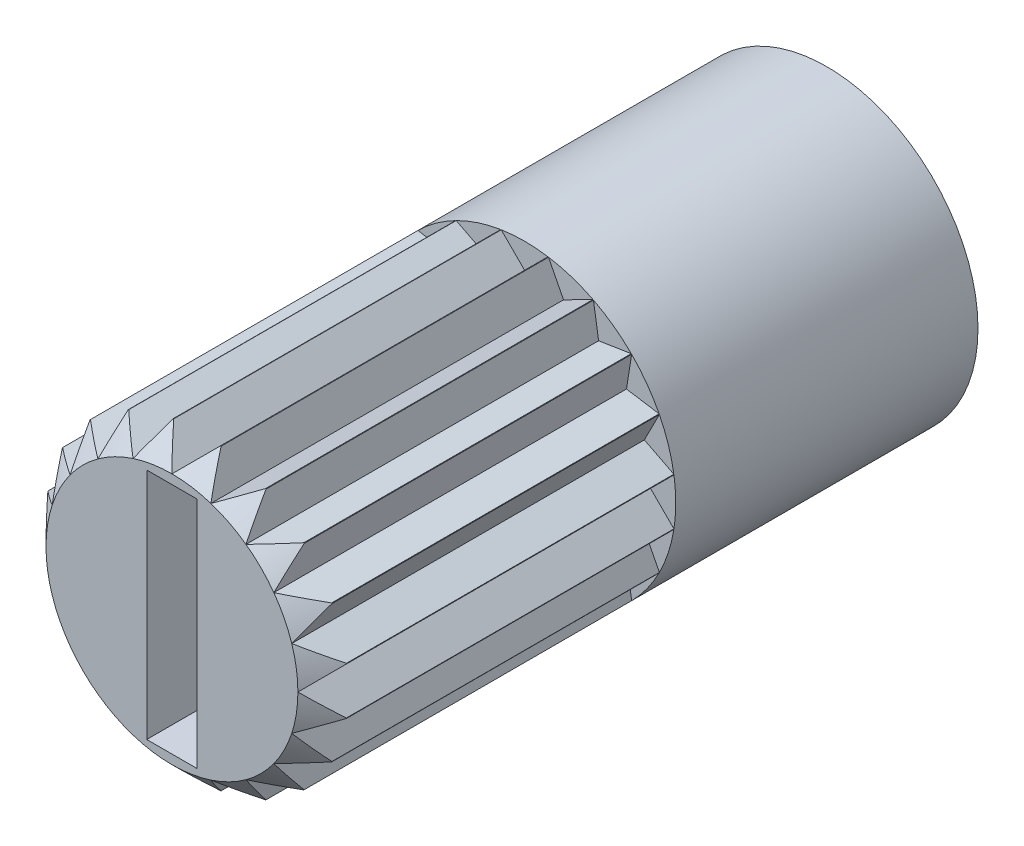
SolidWorks part; units mm, degrees
ref_plane "Plan de face" through (0, 0, 0) normal (0, 0, 1) x (1, 0, 0)
ref_plane "Plan de dessus" through (0, 0, 0) normal (0, 1, 0) x (1, 0, 0)
ref_plane "Plan de droite" through (0, 0, 0) normal (1, 0, 0) x (0, 0, -1)
sketch "Esquisse1" plane through (0, 0, 0) normal (0, 0, 1) x (1, 0, 0)
  circle A0 centre (0, 0) radius 3
  dimension "D1" = 6
extrude "Boss.-Extru.1" add sketch "Esquisse1" along normal blind 3 and the other way blind 10
sketch "Esquisse3" plane through (0, 0, 3) normal (0, 0, 1) x (1, 0, 0)
  line L0 (0, -3.4377) -> (0, 2.4248) construction
  line L1 (-3.9874, 0) -> (3.549, 0) construction
  line L2 (-0.5, 2.3162) -> (0.5, 2.3162)
  line L3 (-0.5, 2.3162) -> (-0.5, -2.3162)
  line L4 (-0.5, -2.3162) -> (0.5, -2.3162)
  line L5 (0.5, 2.3162) -> (0.5, -2.3162)
  dimension "D1" = 1
  dimension "D2" = 0.1086
extrude "Enlèv. mat.-Extru.2" cut sketch "Esquisse3" against normal blind 1.5
chamfer "Chanfrein1" distance 0.5 1 edges at (3, 0, 3)
sketch "Esquisse4" plane through (0, 0, 3) normal (0, 0, 1) x (1, 0, 0)
  line L0 (-3.6113, 0) -> (3.6829, 0) construction
  line L1 (-2.9705, -0.4705) -> (-2.5, 0)
  line L2 (-2.5, 0) -> (-2.9705, 0.4705)
  line L3 (-2.3776, 0.7725) -> (-2.6797, 1.3654)
  line L4 (-2.9705, 0.4705) -> (-2.3776, 0.7725)
  line L5 (-2.0225, 1.4695) -> (-2.1266, 2.1266)
  line L6 (-2.6797, 1.3654) -> (-2.0225, 1.4695)
  line L7 (-1.4695, 2.0225) -> (-1.3654, 2.6797)
  line L8 (-2.1266, 2.1266) -> (-1.4695, 2.0225)
  line L10 (-1.3654, 2.6797) -> (-0.7725, 2.3776)
  line L11 (0, 2.5) -> (0.4705, 2.9705)
  line L12 (-0.4705, 2.9705) -> (0, 2.5)
  line L13 (0.7725, 2.3776) -> (1.3654, 2.6797)
  line L14 (0.4705, 2.9705) -> (0.7725, 2.3776)
  line L15 (1.4695, 2.0225) -> (2.1266, 2.1266)
  line L16 (1.3654, 2.6797) -> (1.4695, 2.0225)
  line L17 (2.0225, 1.4695) -> (2.6797, 1.3654)
  line L18 (2.1266, 2.1266) -> (2.0225, 1.4695)
  line L19 (2.3776, 0.7725) -> (2.9705, 0.4705)
  line L20 (2.6797, 1.3654) -> (2.3776, 0.7725)
  line L21 (2.5, 0) -> (2.9705, -0.4705)
  line L22 (2.9705, 0.4705) -> (2.5, 0)
  line L23 (2.3776, -0.7725) -> (2.6797, -1.3654)
  line L24 (2.9705, -0.4705) -> (2.3776, -0.7725)
  line L25 (2.0225, -1.4695) -> (2.1266, -2.1266)
  line L26 (2.6797, -1.3654) -> (2.0225, -1.4695)
  line L27 (1.4695, -2.0225) -> (1.3654, -2.6797)
  line L28 (2.1266, -2.1266) -> (1.4695, -2.0225)
  line L29 (0.7725, -2.3776) -> (0.4705, -2.9705)
  line L30 (1.3654, -2.6797) -> (0.7725, -2.3776)
  line L31 (0, -2.5) -> (-0.4705, -2.9705)
  line L32 (0.4705, -2.9705) -> (0, -2.5)
  line L33 (-0.7725, -2.3776) -> (-1.3654, -2.6797)
  line L34 (-0.4705, -2.9705) -> (-0.7725, -2.3776)
  line L35 (-1.4695, -2.0225) -> (-2.1266, -2.1266)
  line L36 (-1.3654, -2.6797) -> (-1.4695, -2.0225)
  line L37 (-2.0225, -1.4695) -> (-2.6797, -1.3654)
  line L38 (-2.1266, -2.1266) -> (-2.0225, -1.4695)
  line L39 (-2.3776, -0.7725) -> (-2.9705, -0.4705)
  line L40 (-2.6797, -1.3654) -> (-2.3776, -0.7725)
  line L41 (-0.7725, 2.3776) -> (-0.4705, 2.9705)
  line L42 (-1.984, 0) -> (-1.448, 1.052) [skipped]
  circle A0 centre (0, 0) radius 3.4419
  point P69 (0, 0)
  dimension "D2" = 20
  dimension "D1" = 2.5
extrude "Enlèv. mat.-Extru.3" cut sketch "Esquisse4" against normal blind 7
